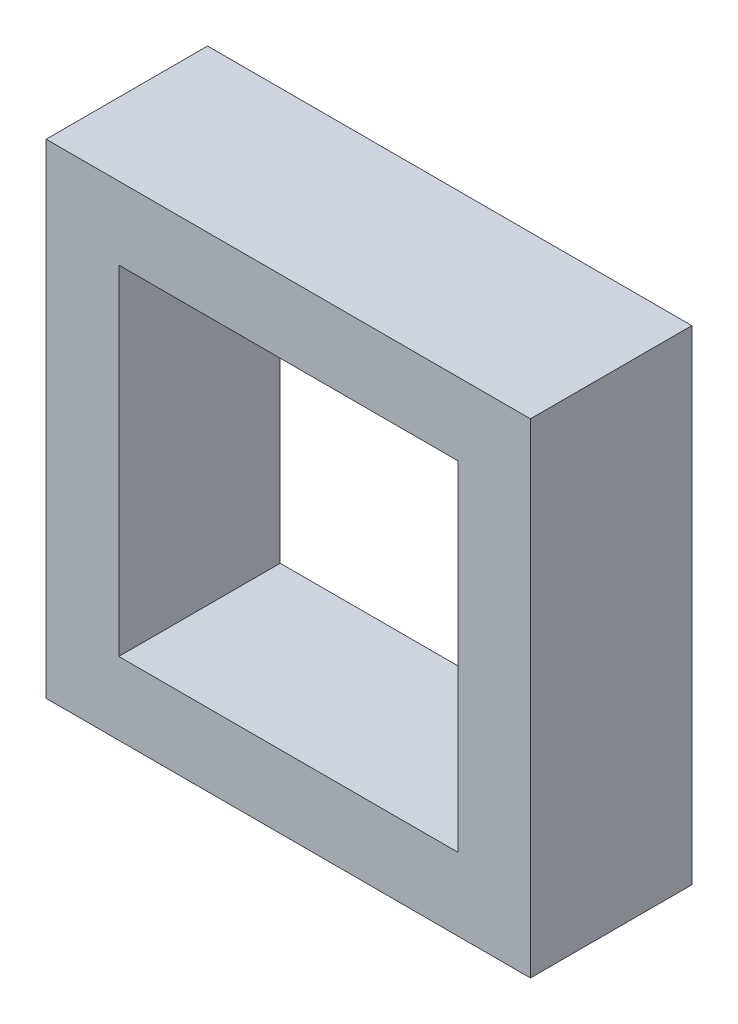
SolidWorks part; units mm, degrees
material "ABS"
ref_plane "Front Plane" through (0, 0, 0) normal (0, 0, 1) x (1, 0, 0)
ref_plane "Top Plane" through (0, 0, 0) normal (0, 1, 0) x (1, 0, 0)
ref_plane "Right Plane" through (0, 0, 0) normal (1, 0, 0) x (0, 0, -1)
sketch "Sketch1" plane through (0, 0, 0) normal (0, 0, 1) x (1, 0, 0)
  line L1 (0, 0) -> (4.2, 0)
  line L2 (0, 0) -> (0, 4.2)
  line L3 (0, 4.2) -> (4.2, 4.2)
  line L4 (4.2, 0) -> (4.2, 4.2)
  line L5 (5.1, 5.1) -> (-0.9, 5.1)
  line L6 (5.1, 5.1) -> (5.1, -0.9)
  line L7 (5.1, -0.9) -> (-0.9, -0.9)
  line L8 (-0.9, 5.1) -> (-0.9, -0.9)
  point P9 (2.1, 4.2)
  point P10 (2.1, 5.1)
  point P11 (4.2, 2.1)
  point P12 (5.1, 2.1)
  dimension "D1" = 6
  dimension "D2" = 6
  dimension "D3" = 4.2
  dimension "D4" = 4.2
extrude "Boss-Extrude1" add sketch "Sketch1" along normal blind 2
